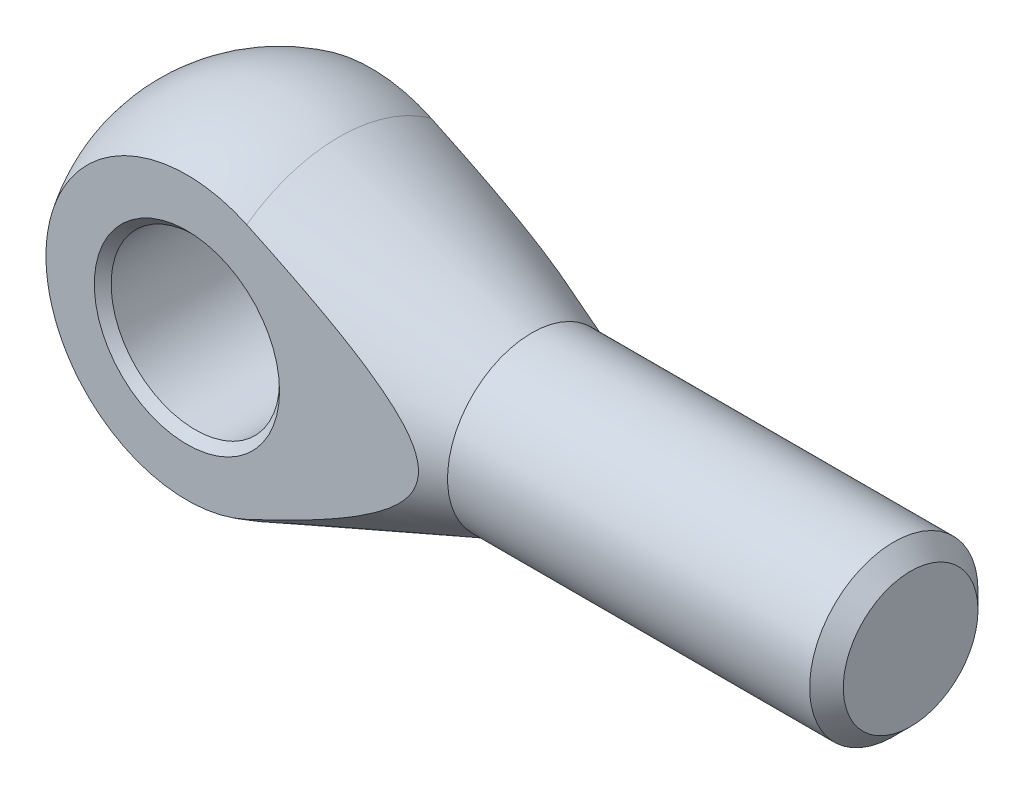
SolidWorks part; units mm, degrees
material "1.2343 (X37CrMoV5-1)"
ref_plane "Nárysná" through (0, 0, 0) normal (0, 0, 1) x (1, 0, 0)
ref_plane "Půdorysná" through (0, 0, 0) normal (0, 1, 0) x (1, 0, 0)
ref_plane "Pravá" through (0, 0, 0) normal (1, 0, 0) x (0, 0, -1)
sketch "Skica1" plane through (0, 0, 0) normal (0, 0, 1) x (1, 0, 0)
  line L0 (7.101, 18.6969) -> (30, 10)
  line L1 (30, 10) -> (75, 10)
  line L2 (75, 10) -> (75, 0)
  line L3 (75, 0) -> (-20, 0)
  line L4 (0, 0) -> (-34.2498, 0) construction
  arc A0 (7.101, 18.6969) -> (-20, 0) centre (0, 0) ccw
  dimension "D1" = 20
  dimension "D2" = 20
  dimension "D3" = 75
  dimension "D4" = 30
revolve "Rotovat1" add sketch "Skica1" angle 360 about L4
cosmetic thread "Kosmetický závit1" parameters "D1"=37, "D2"=17.252
sketch "Skica2" plane through (0, 0, 0) normal (0, 1, 0) x (1, 0, 0)
  line L1 (-65.8109, 10.95) -> (94.9402, 10.95)
  line L2 (-65.8109, 10.95) -> (-65.8109, -10.95)
  line L3 (-65.8109, -10.95) -> (94.9402, -10.95)
  line L4 (94.9402, 10.95) -> (94.9402, -10.95)
  point P4 (-65.8109, 0)
  dimension "D1" = 21.9
extrude "Odebrat vysunutím1" cut sketch "Skica2" against normal through all both and the other way through all flip side to cut
sketch "Skica3" plane through (0, 0, 0) normal (0, 0, 1) x (1, 0, 0)
  circle A0 centre (0, 0) radius 10
  dimension "D1" = 20
extrude "Odebrat vysunutím2" cut sketch "Skica3" against normal through all both and the other way through all
chamfer "Zkosení1" distance 1 angle 45 2 edges at (10, 0, 10.95) (10, 0, -10.95)
chamfer "Zkosení2" distance 2 angle 45 1 edges at (75, 0, -10)
